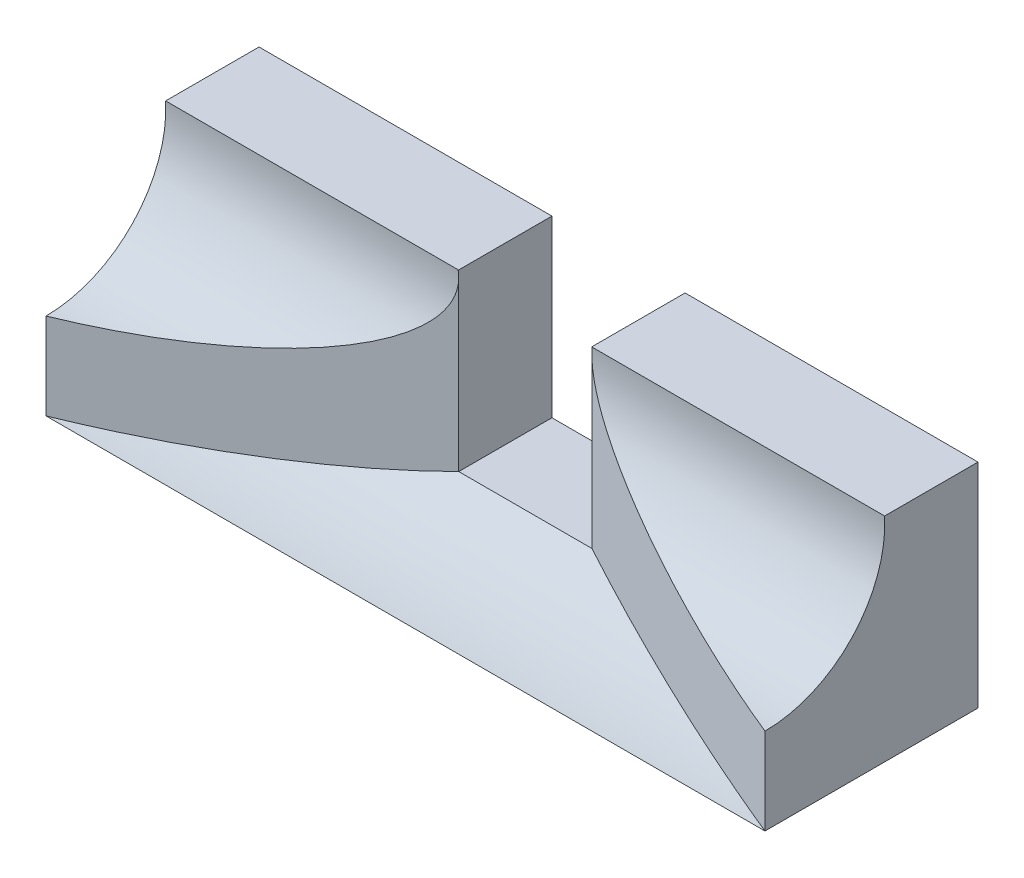
SolidWorks part; units mm, degrees
ref_plane "Front Plane" through (0, 0, 0) normal (0, 0, 1) x (1, 0, 0)
ref_plane "Top Plane" through (0, 0, 0) normal (0, 1, 0) x (1, 0, 0)
ref_plane "Right Plane" through (0, 0, 0) normal (1, 0, 0) x (0, 0, -1)
sketch "Sketch1" plane through (0, 0, 0) normal (0, 1, 0) x (1, 0, 0)
  line L1 (-135, 40) -> (135, 40)
  line L2 (-135, 40) -> (-135, -40)
  line L3 (-135, -40) -> (135, -40)
  line L4 (135, 40) -> (135, -40)
  line L5 (-135, 40) -> (135, -40) construction
  line L6 (-135, -40) -> (135, 40) construction
  point P0 (0, 0)
  dimension "D1" = 270
  dimension "D2" = 80
extrude "Boss-Extrude1" add sketch "Sketch1" along normal blind 80
sketch "Sketch2" plane through (0, 80, 0) normal (0, 1, 0) x (1, 0, 0)
  line L0 (0, 40) -> (0, -40) construction
  line L1 (135, 40) -> (-135, 40) construction
  line L2 (-135, -40) -> (135, -40) construction
  line L3 (25, 5) -> (-25, 5)
  line L4 (-25, 5) -> (-135, -40)
  line L5 (-135, -40) -> (135, -40)
  line L6 (0, -40) -> (0, 5)
  line L7 (25, 5) -> (135, -40)
  line M4 (-135, -40) -> (135, -40)
  dimension "D1" = 45
  dimension "D2" = 50
extrude "Cut-Extrude1" cut sketch "Sketch2" against normal through all contours L6 L3 L4 M4 | L7 L3 L6 L5
sketch "Sketch4" plane through (135, 0, 0) normal (1, 0, 0) x (0, 0, -1)
  line L0 (-40, 80) -> (-40, 0) construction
  line L1 (-40, 0) -> (40, 0) construction
  line L2 (40, 80) -> (37.4597, 80)
  line L3 (40, 80) -> (40, 0)
  line L4 (40, 0) -> (-40, 0)
  arc A0 (-40, 0) -> (37.4597, 80) centre (-40, 77.5) ccw
  circle A1 centre (-40, 77.5) radius 40 construction
  point P9 (-40, 37.5)
  dimension "D1" = 80
  dimension "D2" = 37.5
extrude "Boss-Extrude2" add sketch "Sketch4" against normal up to surface (270 mm away) up to face at (-135, 40, 0)
sketch "Sketch3" plane through (135, 0, 0) normal (1, 0, 0) x (0, 0, -1)
  line L3 (-40, 80) -> (-40, 0) construction
  circle A0 centre (-40, 77.5) radius 40 construction
  circle A1 centre (-40, 77.5) radius 45
  point P2 (-40, 37.5)
  dimension "D1" = 80
  dimension "D2" = 90
  dimension "D3" = 37.5
extrude "Cut-Extrude2" cut sketch "Sketch3" against normal through all
sketch "Sketch5" plane through (0, 0, -5) normal (0, 0, 1) x (1, 0, 0)
  line L1 (-25, 14.4029) -> (25, 14.4029)
  line L2 (-25, 14.4029) -> (-25, 80)
  line L3 (-25, 80) -> (25, 80)
  line L4 (25, 14.4029) -> (25, 80)
extrude "Cut-Extrude3" cut sketch "Sketch5" against normal through all
